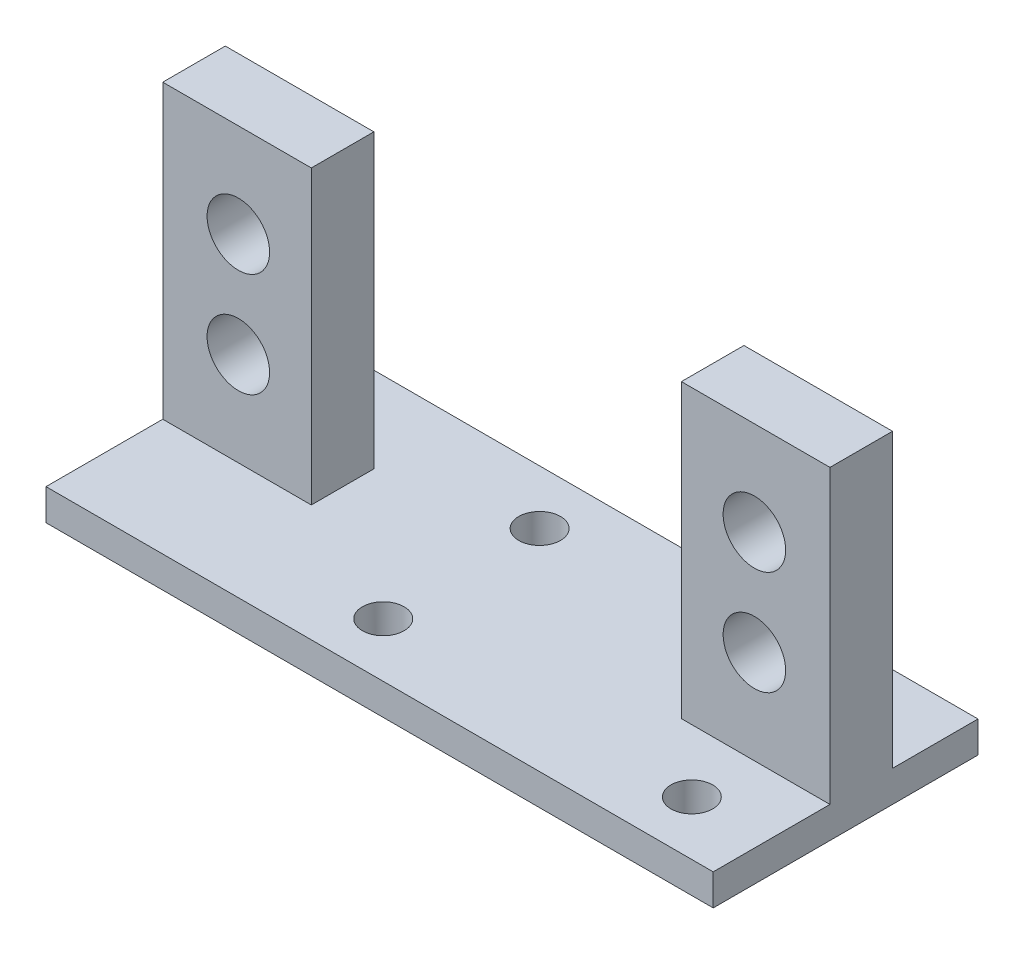
SolidWorks part; units mm, degrees
ref_plane "Front" through (0, 0, 0) normal (0, 0, 1) x (1, 0, 0)
ref_plane "Top" through (0, 0, 0) normal (0, 1, 0) x (1, 0, 0)
ref_plane "Right" through (0, 0, 0) normal (1, 0, 0) x (0, 0, -1)
sketch "草图1" plane through (0, 0, 0) normal (0, 1, 0) x (1, 0, 0)
  line L0 (0, 0) -> (0, 12.7) construction
  line L1 (0, 0) -> (0, -12.7) construction
  line L2 (0, 0) -> (29, 0) construction
  line L3 (-29, 12.7) -> (29, 12.7)
  line L4 (29, 12.7) -> (29, -12.7)
  line L5 (-29, 12.7) -> (-29, -12.7)
  line L6 (-29, -12.7) -> (29, -12.7)
  point P10 (-29, 0)
extrude "凸台-拉伸1" add sketch "草图1" along normal blind 3
sketch "草图2" plane through (0, 3, 0) normal (0, 1, 0) x (1, 0, 0)
  line L0 (0, 12.7) -> (24.75, 12.7) construction
  line L1 (29, 12.7) -> (-29, 12.7) construction
  line L2 (0, 12.7) -> (-24.75, 12.7) construction
  line L3 (-24.75, 12.7) -> (-24.75, 9.7) construction
  line L4 (-24.75, 9.7) -> (-28.75, 9.7) construction
  line L5 (-24.75, 9.7) -> (-20.75, 9.7) construction
  line L6 (24.75, 12.7) -> (24.75, 9.7) construction
  line L7 (24.75, 9.7) -> (28.75, 9.7) construction
  line L8 (24.75, 9.7) -> (20.75, 9.7) construction
  line L9 (-20.75, 9.7) -> (-28.75, 9.7)
  line L10 (-28.75, 9.7) -> (-28.75, 12.7)
  line L11 (-28.75, 12.7) -> (-20.75, 12.7)
  line L12 (-20.75, 12.7) -> (-20.75, 9.7)
  line L13 (20.75, 9.7) -> (28.75, 9.7)
  line L14 (28.75, 9.7) -> (28.75, 12.7)
  line L15 (28.75, 12.7) -> (20.75, 12.7)
  line L16 (20.75, 12.7) -> (20.75, 9.7)
  line L17 (-20.75, 0) -> (-20.75, 1.5) construction
  line L18 (-20.75, 1.5) -> (-28.75, 1.5) construction
  line L19 (-28.75, 1.5) -> (-28.75, -1.5) construction
  line L20 (-28.75, -1.5) -> (-20.75, -1.5) construction
  line L21 (-20.75, -1.5) -> (-20.75, 0) construction
  line L22 (0, 0) -> (0, 4.2412) construction
  line L23 (-28.75, 1.5) -> (-20.75, 1.5)
  line L24 (-20.75, 1.5) -> (-20.75, -1.5)
  line L25 (-20.75, -1.5) -> (-28.75, -1.5)
  line L26 (-28.75, -1.5) -> (-28.75, 1.5)
  line L27 (28.75, -1.5) -> (28.75, 1.5)
  line L28 (20.75, -1.5) -> (28.75, -1.5)
  line L29 (20.75, 1.5) -> (20.75, -1.5)
  line L30 (28.75, 1.5) -> (20.75, 1.5)
extrude "凸台-拉伸2" add sketch "草图2" along normal blind 28
sketch "草图3" plane through (0, 0, -9.7) normal (0, 0, 1) x (1, 0, 0)
  line L0 (-24.75, 17) -> (-20.75, 17) construction
  line L2 (-24.75, 17) -> (-24.75, 22) construction
  line L3 (-20.75, 31) -> (-20.75, 3) construction
  line L4 (-24.75, 17) -> (-24.75, 12) construction
  line L5 (0, 0) -> (0, 3) construction
  line L6 (-29, 3) -> (29, 3) construction
  circle A0 centre (-24.75, 12) radius 3
  circle A1 centre (-24.75, 22) radius 3
  circle A2 centre (24.75, 12) radius 3
  circle A3 centre (24.75, 22) radius 3
extrude "切除-拉伸1" cut sketch "草图3" against normal mid plane 24
sketch "草图4" plane through (0, 3, 0) normal (0, 1, 0) x (1, 0, 0)
  line L0 (0, 0) -> (24.75, 0) construction
  line L1 (24.75, 0) -> (24.75, 12.7) construction
  line L2 (28.75, 12.7) -> (20.75, 12.7) construction
  line L3 (24.75, 12.7) -> (9.95, 12.7) construction
  line L4 (20.75, 12.7) -> (-20.75, 12.7) construction
  line L5 (9.95, 12.7) -> (9.95, 0) construction
  line L6 (9.95, 0) -> (9.95, -12.7) construction
  line L7 (-29, -12.7) -> (29, -12.7) construction
  line L8 (9.95, 6.35) -> (-4.85, 6.35) construction
  line L9 (24.75, 0) -> (24.75, -7.5) construction
  circle A4 centre (24.75, -7.5) radius 2
  circle A5 centre (24.75, 7.5) radius 2
  circle A6 centre (-4.85, 7.5) radius 2
  circle A7 centre (-4.85, -7.5) radius 2
extrude "切除-拉伸2" cut sketch "草图4" against normal blind 22
sketch "草图5" plane through (0, 31, 0) normal (0, 1, 0) x (1, 0, 0)
  line L0 (-28.75, 12.7) -> (-28.75, 9.7)
  line L1 (-28.75, 9.7) -> (-20.75, 9.7)
  line L2 (-20.75, 9.7) -> (-20.75, 12.7)
  line L3 (-20.75, 12.7) -> (-28.75, 12.7)
  line L4 (20.75, 12.7) -> (20.75, 9.7)
  line L5 (20.75, 9.7) -> (28.75, 9.7)
  line L6 (28.75, 9.7) -> (28.75, 12.7)
  line L7 (28.75, 12.7) -> (20.75, 12.7)
extrude "切除-拉伸3" cut sketch "草图5" against normal blind 28
sketch "草图6" plane through (0, 0, -1.5) normal (0, 0, -1) x (-1, 0, 0)
  line L0 (-28.75, 3) -> (-28.75, 31)
  line L1 (-28.75, 31) -> (-20.75, 31)
  line L2 (-20.75, 31) -> (-20.75, 3)
  line L3 (-20.75, 3) -> (-28.75, 3)
  line L4 (20.75, 31) -> (28.75, 31)
  line L5 (28.75, 31) -> (28.75, 3)
  line L6 (28.75, 3) -> (20.75, 3)
  line L7 (20.75, 3) -> (20.75, 31)
  circle A0 centre (-24.75, 22) radius 3
  circle A1 centre (-24.75, 12) radius 3
  circle A2 centre (24.75, 22) radius 3
  circle A3 centre (24.75, 12) radius 3
extrude "凸台-拉伸3" add sketch "草图6" along normal blind 3
sketch "草图7" plane through (20.75, 0, 0) normal (-1, 0, 0) x (0, 0, 1)
  line L0 (-4.5, 31) -> (1.5, 31)
  line L1 (1.5, 31) -> (1.5, 3)
  line L3 (1.5, 3) -> (-4.5, 3)
  line L4 (-4.5, 3) -> (-4.5, 31)
extrude "凸台-拉伸4" add sketch "草图7" along normal blind 3
sketch "草图8" plane through (-20.75, 0, 0) normal (1, 0, 0) x (0, 0, -1)
  line L0 (-1.5, 31) -> (4.5, 31)
  line L1 (4.5, 31) -> (4.5, 3)
  line L2 (4.5, 3) -> (-1.5, 3)
  line L3 (-1.5, 3) -> (-1.5, 31)
extrude "凸台-拉伸5" add sketch "草图8" along normal blind 3
sketch "草图9" plane through (28.75, 0, 0) normal (1, 0, 0) x (0, 0, -1)
  line L0 (-1.5, 31) -> (4.5, 31)
  line L1 (4.5, 31) -> (4.5, 3)
  line L2 (4.5, 3) -> (-1.5, 3)
  line L3 (-1.5, 3) -> (-1.5, 31)
extrude "凸台-拉伸6" add sketch "草图9" along normal blind 0.25
sketch "草图10" plane through (-28.75, 0, 0) normal (-1, 0, 0) x (0, 0, 1)
  line L0 (-4.5, 31) -> (1.5, 31)
  line L1 (1.5, 31) -> (1.5, 3)
  line L2 (1.5, 3) -> (-4.5, 3)
  line L3 (-4.5, 3) -> (-4.5, 31)
extrude "凸台-拉伸7" add sketch "草图10" along normal blind 0.25
sketch "草图11" plane through (-29, 0, 0) normal (-1, 0, 0) x (0, 0, 1)
  line L0 (-4.5, 31) -> (1.5, 31)
  line L1 (1.5, 31) -> (1.5, 3)
  line L2 (1.5, 3) -> (12.7, 3)
  line L3 (12.7, 3) -> (12.7, 0)
  line L4 (12.7, 0) -> (-12.7, 0)
  line L5 (-12.7, 0) -> (-12.7, 3)
  line L6 (-12.7, 3) -> (-4.5, 3)
  line L7 (-4.5, 3) -> (-4.5, 31)
extrude "凸台-拉伸8" add sketch "草图11" along normal blind 3
sketch "草图12" plane through (29, 0, 0) normal (1, 0, 0) x (0, 0, -1)
  line L0 (-1.5, 31) -> (4.5, 31)
  line L1 (4.5, 31) -> (4.5, 3)
  line L2 (4.5, 3) -> (12.7, 3)
  line L3 (12.7, 3) -> (12.7, 0)
  line L4 (12.7, 0) -> (-12.7, 0)
  line L5 (-12.7, 0) -> (-12.7, 3)
  line L6 (-12.7, 3) -> (-1.5, 3)
  line L7 (-1.5, 3) -> (-1.5, 31)
extrude "凸台-拉伸9" add sketch "草图12" along normal blind 3
